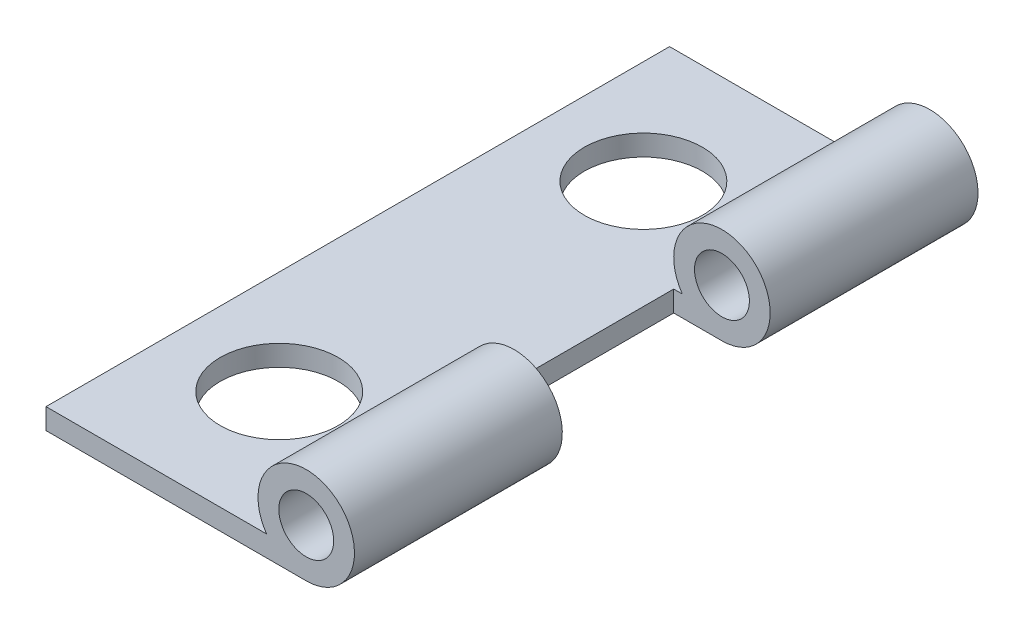
SolidWorks part; units mm, degrees
ref_plane "Front Plane" through (0, 0, 0) normal (0, 0, 1) x (1, 0, 0)
ref_plane "Top Plane" through (0, 0, 0) normal (0, 1, 0) x (1, 0, 0)
ref_plane "Right Plane" through (0, 0, 0) normal (1, 0, 0) x (0, 0, -1)
sketch "Sketch1" plane through (0, 0, 0) normal (0, 0, 1) x (1, 0, 0)
  line L4 (-1.5423, 2.9903) -> (-1.5423, 1.6367) construction
  line L5 (-1.5423, 1.6367) -> (-1.5423, -4.5326) construction
  line L6 (-11.0349, 1.6367) -> (-11.0349, 2.2717)
  line L7 (-11.0349, 2.2717) -> (-4.2962, 2.2717)
  line L8 (-11.0349, 1.6367) -> (-3.0847, 1.6367)
  circle A2 centre (-3.0847, 3.1099) radius 0.8382
  arc A3 (-3.0847, 1.6367) -> (-4.2962, 2.2717) centre (-3.0847, 3.1099) ccw
  point P11 (-7.9502, 1.6367)
  point P17 (-7.9502, 2.4317)
  point P18 (-1.5423, 2.9903)
  dimension "D2" = 1.6764
  dimension "D3" = 1.4732
  dimension "D1" = 7.9502
  dimension "D4" = 0.635
extrude "Boss-Extrude1" add sketch "Sketch1" along normal blind 19.05
sketch "Sketch2" plane through (0, 0, 0) normal (0, 0, -1) x (-1, 0, 0)
  circle A0 centre (3.0847, 3.1099) radius 2.4638
sketch "Sketch7" plane through (0, 2.2717, 0) normal (0, 1, 0) x (1, 0, 0)
  line L4 (-4.2962, 0) -> (-11.0349, 0) construction
  circle A0 centre (-7.8725, -3.9624) radius 1.8034
  circle A1 centre (-7.8725, -15.0876) radius 1.8034
  dimension "D1" = 11.1252
  dimension "D4" = 3.6068
  dimension "D2" = 3.9624
extrude "Cut-Extrude5" cut sketch "Sketch7" against normal blind 2.54
sketch "Sketch8" plane through (0, 2.2717, 0) normal (0, 1, 0) x (1, 0, 0)
  line L0 (-4.5579, 0) -> (-4.5579, -19.05) construction
  line L1 (-4.5579, -6.35) -> (-1.6115, -6.35)
  line L2 (-4.5579, -6.35) -> (-4.5579, -12.7)
  line L3 (-4.5579, -12.7) -> (-1.6115, -12.7)
  line L4 (-1.6115, -6.35) -> (-1.6115, -12.7)
  line L6 (-0.6209, 0) -> (-5.5485, 0) construction
  dimension "D1" = 6.35
  dimension "D2" = 6.35
extrude "Cut-Extrude6" cut sketch "Sketch8" against normal through all both and the other way through all
